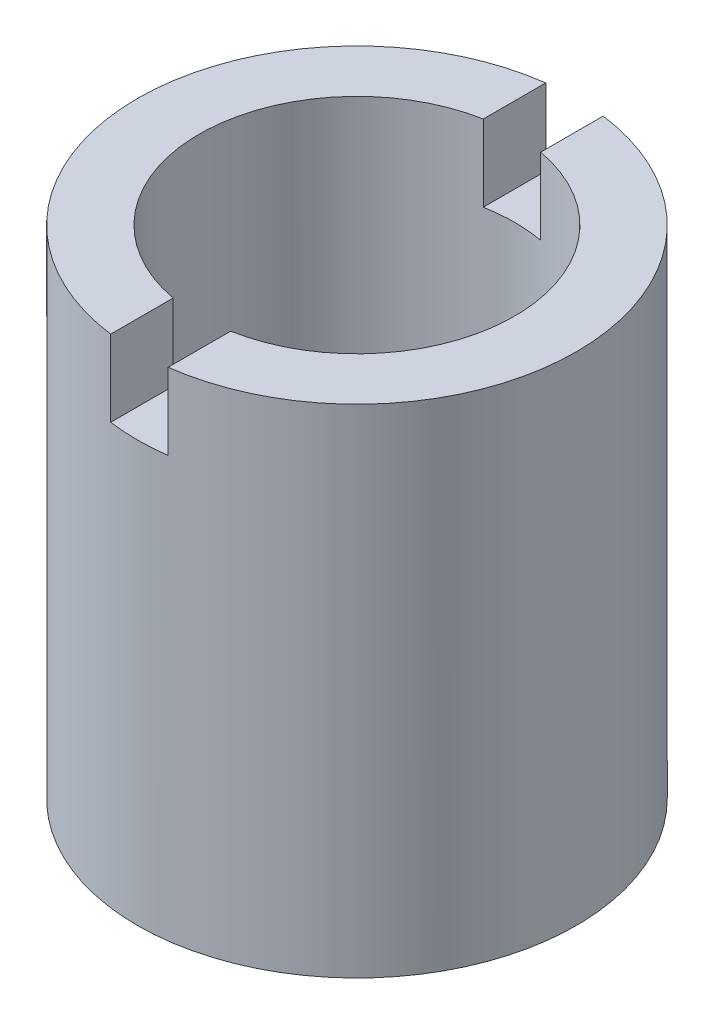
SolidWorks part; units mm, degrees
ref_plane "Front Plane" through (0, 0, 0) normal (0, 0, 1) x (1, 0, 0)
ref_plane "Top Plane" through (0, 0, 0) normal (0, 1, 0) x (1, 0, 0)
ref_plane "Right Plane" through (0, 0, 0) normal (1, 0, 0) x (0, 0, -1)
sketch "Sketch2" plane through (0, 0, 0) normal (0, 1, 0) x (1, 0, 0)
  circle A0 centre (0, 0) radius 6.5532
  circle A1 centre (0, 0) radius 9.1186
  dimension "D1" = 13.1064
  dimension "D2" = 18.2372
extrude "Boss-Extrude1" add sketch "Sketch2" along normal blind 20.6502
sketch "Sketch3" plane through (0, 20.6502, 0) normal (0, 1, 0) x (1, 0, 0)
  line L0 (0, 4.7479) -> (0, -5.0727) construction
  line L5 (1.1938, 4.7479) -> (1.1938, 10.5386)
  line L6 (1.1938, 10.5386) -> (-1.1938, 10.5386)
  line L7 (-1.1938, 10.5386) -> (-1.1938, -10.5885)
  line L8 (-1.1938, -10.5885) -> (1.1938, -10.5885)
  line L9 (1.1938, -10.5885) -> (1.1938, 10.5386)
  point P6 (0, 4.7479)
  circle M2 centre (0, 0) radius 9.1186
  circle M3 centre (0, 0) radius 6.5532
  dimension "D1" = 2.3876
extrude "Cut-Extrude1" cut sketch "Sketch3" against normal blind 3.175 and the other way through all contours L9 L7 M2 M3 | L7 L5 M2 M3
